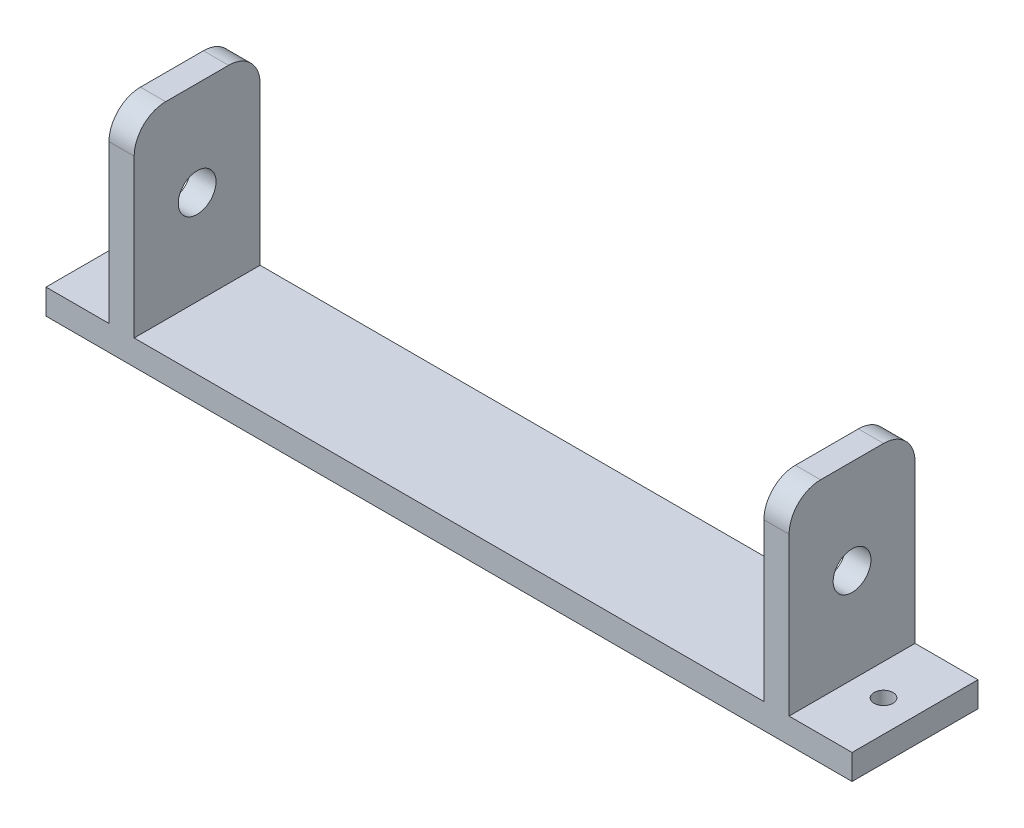
SolidWorks part; units mm, degrees
material "Acrylic (Medium-high impact)"
ref_plane "Front Plane" through (0, 0, 0) normal (0, 0, 1) x (1, 0, 0)
ref_plane "Top Plane" through (0, 0, 0) normal (0, 1, 0) x (1, 0, 0)
ref_plane "Right Plane" through (0, 0, 0) normal (1, 0, 0) x (0, 0, -1)
sketch "Sketch1" plane through (0, 0, 0) normal (0, 0, 1) x (1, 0, 0)
  line L0 (-89.7318, 25.7528) -> (-89.7318, -4.2472)
  line L1 (-89.7318, -4.2472) -> (10.2682, -4.2472)
  line L2 (10.2682, -4.2472) -> (10.2682, 25.7528)
  line L3 (-93.7318, 25.7528) -> (-93.7318, -8.2472)
  line L4 (-93.7318, -8.2472) -> (14.2682, -8.2472)
  line L5 (14.2682, -8.2472) -> (14.2682, 25.7528)
  line L6 (-93.7318, 25.7528) -> (-89.7318, 25.7528)
  line L7 (10.2682, 25.7528) -> (14.2682, 25.7528)
  dimension "D1" = 4
  dimension "D2" = 108
extrude "Boss-Extrude1" add sketch "Sketch1" along normal blind 20
sketch "Sketch2" plane through (-93.7318, 0, 0) normal (-1, 0, 0) x (0, 0, 1)
  line L0 (20, 25.7528) -> (0, 25.7528) construction
  line L1 (0, 25.7528) -> (0, -4.2472) construction
  line L2 (0, 25.7528) -> (0, -8.2472) construction
  circle A0 centre (10, 10.7528) radius 3
  dimension "D1" = 15
  dimension "D2" = 10
extrude "Cut-Extrude1" cut sketch "Sketch2" against normal blind 4
sketch "Sketch3" plane through (14.2682, 0, 0) normal (1, 0, 0) x (0, 0, -1)
  line L0 (-20, -8.2472) -> (-20, 25.7528) construction
  line L1 (-20, 25.7528) -> (0, 25.7528) construction
  circle A0 centre (-10, 10.7528) radius 3
  dimension "D1" = 10
  dimension "D2" = 15
extrude "Cut-Extrude2" cut sketch "Sketch3" against normal blind 4
fillet "Fillet1" radius 5 4 edges at (12.2682, 25.7528, 0) (-91.7318, 25.7528, 20) (-91.7318, 25.7528, 0) (12.2682, 25.7528, 20)
sketch "Sketch4" plane through (14.2682, 0, 0) normal (1, 0, 0) x (0, 0, -1)
  line L1 (-20, -8.2472) -> (0, -8.2472)
  line L2 (-20, -8.2472) -> (-20, -4.2472)
  line L3 (-20, -4.2472) -> (0, -4.2472)
  line L4 (0, -8.2472) -> (0, -4.2472)
extrude "Boss-Extrude2" add sketch "Sketch4" along normal blind 10
sketch "Sketch5" plane through (-93.7318, 0, 0) normal (-1, 0, 0) x (0, 0, 1)
  line L1 (0, -8.2472) -> (20, -8.2472)
  line L2 (0, -8.2472) -> (0, -4.2472)
  line L3 (0, -4.2472) -> (20, -4.2472)
  line L4 (20, -8.2472) -> (20, -4.2472)
extrude "Boss-Extrude3" add sketch "Sketch5" along normal blind 10
sketch "Sketch6" plane through (0, -4.2472, 0) normal (0, 1, 0) x (1, 0, 0)
  line L0 (-103.7318, -20) -> (-93.7318, -20) construction
  line L1 (-103.7318, -20) -> (-103.7318, 0) construction
  line L2 (24.2682, -20) -> (14.2682, -20) construction
  line L3 (24.2682, 0) -> (24.2682, -20) construction
  circle A0 centre (-98.7318, -10) radius 1.5
  circle A1 centre (19.2682, -10) radius 1.5
  dimension "D1" = 10
  dimension "D2" = 5
  dimension "D3" = 10
  dimension "D4" = 5
extrude "Cut-Extrude3" cut sketch "Sketch6" against normal blind 4
